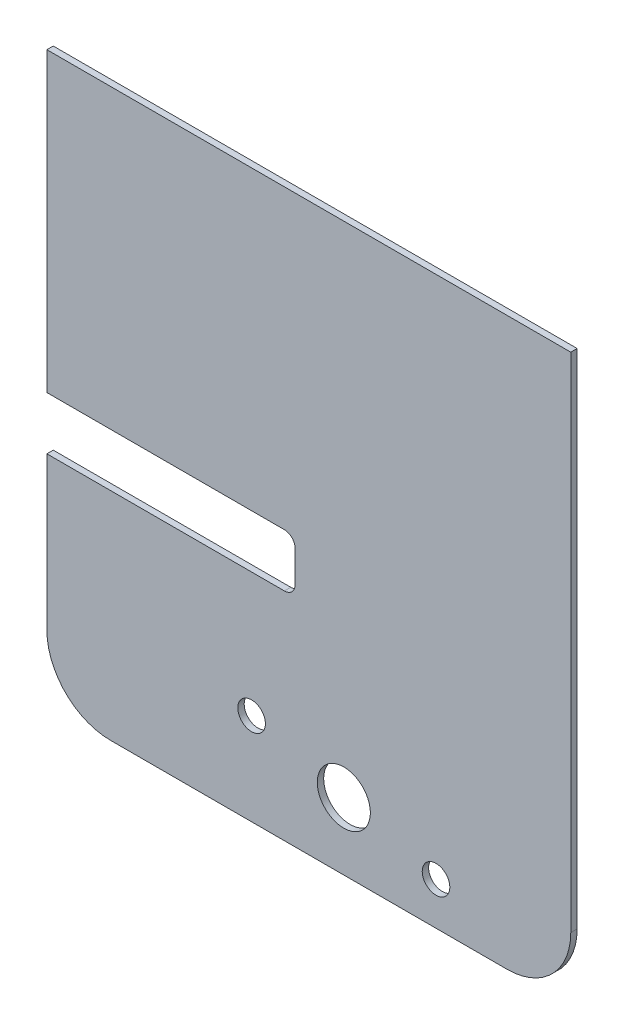
SolidWorks part; units mm, degrees
ref_plane "Plan de face" through (0, 0, 0) normal (0, 0, 1) x (1, 0, 0)
ref_plane "Plan de dessus" through (0, 0, 0) normal (0, 1, 0) x (1, 0, 0)
ref_plane "Plan de droite" through (0, 0, 0) normal (1, 0, 0) x (0, 0, -1)
sketch "Esquisse1" plane through (0, 0, 0) normal (0, 0, 1) x (1, 0, 0)
  line L1 (-123.5, -133.5) -> (123.5, -133.5)
  line L2 (-123.5, -133.5) -> (-123.5, 133.5)
  line L3 (-123.5, 133.5) -> (123.5, 133.5)
  line L4 (123.5, -133.5) -> (123.5, 133.5)
  line L5 (-123.5, -133.5) -> (123.5, 133.5) construction
  line L6 (-123.5, 133.5) -> (123.5, -133.5) construction
  point P0 (0, 0)
  dimension "D1" = 247
  dimension "D2" = 267
extrude "Boss.-Extru.1" add sketch "Esquisse1" along normal blind 3
sketch "Esquisse2" plane through (0, 0, 3) normal (0, 0, 1) x (1, 0, 0)
  line L6 (-123.5, 133.5) -> (-123.5, -133.5) construction
  line L11 (-123.5, 48.5) -> (-120.5, 48.5)
  line L12 (-123.5, 48.5) -> (-123.5, -31.5)
  line L13 (-123.5, -31.5) -> (-120.5, -31.5)
  line L14 (-120.5, 48.5) -> (-120.5, -31.5)
  line L15 (123.5, 133.5) -> (-123.5, 133.5) construction
  line L17 (-123.5, 133.5) -> (-48.5, 133.5)
  line L18 (-123.5, 133.5) -> (-123.5, 130.5)
  line L19 (-123.5, 130.5) -> (-48.5, 130.5)
  line L20 (-48.5, 133.5) -> (-48.5, 130.5)
  line L21 (123.5, 133.5) -> (48.5, 133.5)
  line L22 (123.5, 133.5) -> (123.5, 130.5)
  line L23 (123.5, 130.5) -> (48.5, 130.5)
  line L24 (48.5, 133.5) -> (48.5, 130.5)
  dimension "D1" = 3
  dimension "D2" = 85
  dimension "D3" = 80
  dimension "D4" = 3
  dimension "D5" = 75
  dimension "D6" = 75
extrude "Enlèv. mat.-Extru.1" [suppressed] cut sketch "Esquisse2" against normal blind 3
sketch "Esquisse3" plane through (0, 0, 0) normal (0, 0, -1) x (-1, 0, 0)
  line L0 (-70.8887, -116.4266) -> (18.4777, -92.4809) construction
  line L1 (123.5, -133.5) -> (-123.5, -133.5) construction
  line L2 (123.5, 133.5) -> (123.5, -133.5) construction
  circle A0 centre (-59.9667, -113.5) radius 6.5
  circle A1 centre (-16.5, -101.8531) radius 12.5
  circle A2 centre (26.9667, -90.2063) radius 6.5
  dimension "D1" = 13
  dimension "D2" = 25
  dimension "D3" = 45
  dimension "D4" = 90
  dimension "D5" = 20
  dimension "D6" = 15
  dimension "D7" = 140
extrude "Enlèv. mat.-Extru.2" cut sketch "Esquisse3" against normal blind 3
sketch "Esquisse4" plane through (0, 0, 0) normal (0, 0, -1) x (-1, 0, 0)
  line L1 (126.5, -31.5) -> (6.5, -31.5)
  line L2 (126.5, -31.5) -> (126.5, -6.5)
  line L3 (126.5, -6.5) -> (6.5, -6.5)
  line L4 (6.5, -31.5) -> (6.5, -6.5)
  dimension "D1" = 25
  dimension "D2" = 120
extrude "Enlèv. mat.-Extru.3" cut sketch "Esquisse4" against normal blind 10
fillet "Congé1" radius 30 2 edges at (-123.5, -133.5, 1.5) (123.5, -133.5, 1.5)
fillet "Congé2" radius 5 2 edges at (-6.5, -31.5, 1.5) (-6.5, -6.5, 1.5)
